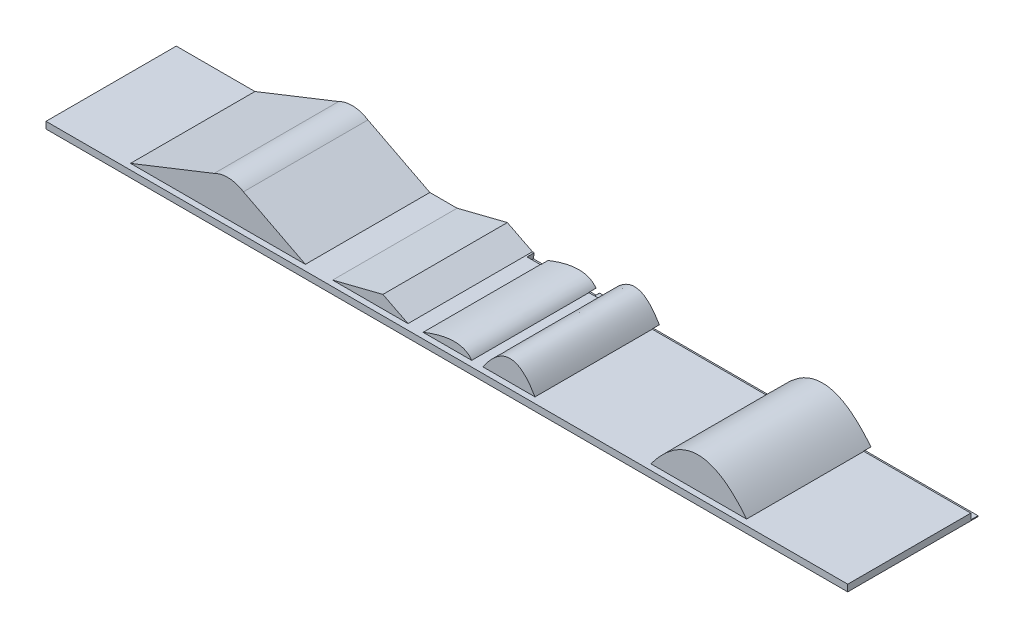
SolidWorks part; units mm, degrees
material "Balsa"
ref_plane "Front Plane" through (0, 0, 0) normal (0, 0, 1) x (1, 0, 0)
ref_plane "Top Plane" through (0, 0, 0) normal (0, 1, 0) x (1, 0, 0)
ref_plane "Right Plane" through (0, 0, 0) normal (1, 0, 0) x (0, 0, -1)
sketch "Sketch1" plane through (0, 0, 0) normal (0, 1, 0) x (1, 0, 0)
  line L1 (-2000, 325) -> (2000, 325)
  line L2 (-2000, 325) -> (-2000, -325)
  line L3 (-2000, -325) -> (2000, -325)
  line L4 (2000, 325) -> (2000, -325)
  line L5 (-2000, 325) -> (2000, -325) construction
  line L6 (-2000, -325) -> (2000, 325) construction
  point P0 (0, 0)
  dimension "D1" = 4000
  dimension "D2" = 650
extrude "Boss-Extrude1" add sketch "Sketch1" along normal blind 300
sketch "Sketch3" plane through (0, 0, -325) normal (0, 0, -1) x (-1, 0, 0)
  line L1 (-2000, 4.3951) -> (-154.7908, 4.3951)
  line L2 (-2000, 300) -> (-2000, 0) construction
  line L3 (-96.042, 4.7676) -> (24.2868, 4.7676)
  line L4 (142.8684, 5.4882) -> (218.4529, 5.4882)
  line L5 (-2000, 4.3951) -> (-2000, 34.4547)
  line L6 (-2000, 34.4547) -> (213.9269, 34.4547)
  line L7 (213.9269, 34.4547) -> (218.4529, 5.4882)
  spline S0 degree 3 poles (-154.7908, 4.3951) (-122.1212, 28.8494) (-111.5629, 29.4861) (-96.042, 4.7676) knots 0 0 0 0 1 1 1 1
  spline S1 degree 2 poles (24.2868, 4.7676) (43.5204, 22.639) (73.6204, 4.583) knots 0 0 0 1 1 1
  spline S2 degree 3 poles (73.6204, 4.583) (101.9041, 17.0278) (102.6454, 9.5282) (123.3234, 0.5599) (134.3864, 12.8392) (142.8684, 5.4882) knots 0 0 0 0 0.498478 0.598478 1 1 1 1
sketch "Sketch4" plane through (0, 0, 325) normal (0, 0, 1) x (1, 0, 0)
  line L0 (-2000, 42) -> (-1023.9204, 42)
  line L1 (-2000, 300) -> (-2000, 0) construction
  line L2 (-394.069, 42) -> (77.2814, 42)
  line L3 (1331.8132, 42) -> (2000, 42)
  line L4 (2000, 300) -> (2000, 0) construction
  line L5 (-2000, 42) -> (-2000, 300)
  line L6 (-2000, 300) -> (2000, 300)
  line L7 (2000, 300) -> (2000, 42)
  line L8 (-2000, 0) -> (2000, 0) construction
  spline S0 degree 3 poles (-1023.9204, 42) (-625.5961, 421.2901) (-564.5006, 42) (-394.069, 42) knots 0 0 0 0 1 1 1 1
  spline S1 degree 2 poles (77.2814, 42) (384.8208, 379.8759) (804.1429, 42.1625) knots 0 0 0 1 1 1
  spline S2 degree 3 poles (804.1429, 42.1625) (1120.5609, 359.5201) (1155.9231, 42) (1331.8132, 42) knots 0 0 0 0 1 1 1 1
  dimension "D1" = 42
  dimension "D2" = 42
  dimension "D3" = 42
extrude "Cut-Extrude3" cut sketch "Sketch4" against normal blind 333
sketch "Sketch6" plane through (0, 0, -325) normal (0, 0, -1) x (-1, 0, 0)
  line L0 (-2000, 42) -> (-1446.0573, 42)
  line L1 (-2000, 300) -> (-2000, 0) construction
  line L2 (-723.1041, 43.7499) -> (89.9961, 43.7499)
  line L3 (1476.2972, 43.7499) -> (2000, 42)
  line L4 (-2000, 0) -> (2000, 0) construction
  line L5 (-2000, 42) -> (-2000, 300)
  line L6 (-2000, 300) -> (2000, 300)
  line L7 (2000, 300) -> (2000, 42)
  spline S0 degree 2 poles (-1446.0573, 42) (-1028.4852, 427.4906) (-723.1041, 43.7499) knots 0 0 0 1 1 1
  spline S1 degree 2 poles (89.9961, 43.7499) (269.6743, 358.5022) (843.0898, 43.7499) knots 0 0 0 1 1 1
  spline S2 degree 2 poles (843.0898, 43.7499) (1192.189, 462.0391) (1476.2972, 43.7499) knots 0 0 0 1 1 1
  dimension "D1" = 0.191
  dimension "D2" = 42
extrude "Cut-Extrude4" cut sketch "Sketch6" against normal blind 333
sketch "Sketch7" plane through (0, 0, 325) normal (0, 0, 1) x (1, 0, 0)
  line L0 (-2000, 42) -> (-2000, 0) construction
  line L1 (-2000, 33.5254) -> (2176.6127, 33.5254)
  line L2 (-2000, 33.5254) -> (-2000, 912.0653)
  line L3 (-2000, 912.0653) -> (2176.6127, 912.0653)
  line L4 (2176.6127, 33.5254) -> (2176.6127, 912.0653)
extrude "Cut-Extrude5" cut sketch "Sketch7" against normal blind 1765
sketch "Sketch8" plane through (0, 0, -325) normal (0, 0, -1) x (-1, 0, 0)
  line L0 (2000, 33.5254) -> (-2000, 33.5254) construction
  line L1 (222.8102, 33.5254) -> (348.1989, 96.9266)
  line L2 (348.1989, 96.9266) -> (598.9762, 33.5254)
  line L3 (734.8295, 33.5254) -> (1043.8809, 192.3333)
  line L4 (1190.0911, 198.922) -> (1607.4877, 33.5254)
  line L5 (-1466.4115, 33.5254) -> (1607.4877, 33.5254)
  arc A0 (1043.8809, 192.3333) -> (1190.0911, 198.922) centre (1122.6704, 69.4859) cw
  spline S0 degree 1 poles (-1499.3042, 33.5254) (-988.6072, 33.5254) knots 0 0 1 1
  spline S1 degree 2 poles (-988.6072, 33.5254) (-1220.1043, 346.5415) (-1466.4115, 33.5254) knots 0 0 0 1 1 1
  spline S2 degree 2 poles (-615.1296, 33.5254) (-519.5063, 140.1435) (-449.6395, 33.5254) knots 0 0 0 1 1 1
  spline S3 degree 2 poles (-410.7439, 33.5254) (-291.4665, 240.9778) (-151.0381, 33.5254) knots 0 0 0 1 1 1
  spline S4 degree 2 poles (-94.9439, 33.5254) (-41.7849, 109.9124) (147.6281, 33.5254) knots 0 0 0 1 1 1
  line M14 (2000, 33.5254) -> (-2000, 33.5254)
extrude "Boss-Extrude2" add sketch "Sketch8" against normal blind 621 contours L5 S1 | S3 L5 | S2 L5 | S4 L5 | L2 L1 M14 | A0 L3 L4 M14
extrude "Cut-Extrude2" cut sketch "Sketch3" against normal blind 36
sketch "Sketch9" plane through (0, 0, -325) normal (0, 0, -1) x (-1, 0, 0)
  line L1 (-615.1296, 33.5254) -> (-438.7747, 33.5254)
  line L2 (-615.1296, 33.5254) -> (-615.1296, 104.488)
  line L3 (-615.1296, 104.488) -> (-438.7747, 104.488)
  line L4 (-438.7747, 33.5254) -> (-438.7747, 104.488)
extrude "Cut-Extrude6" cut sketch "Sketch9" against normal blind 1243
